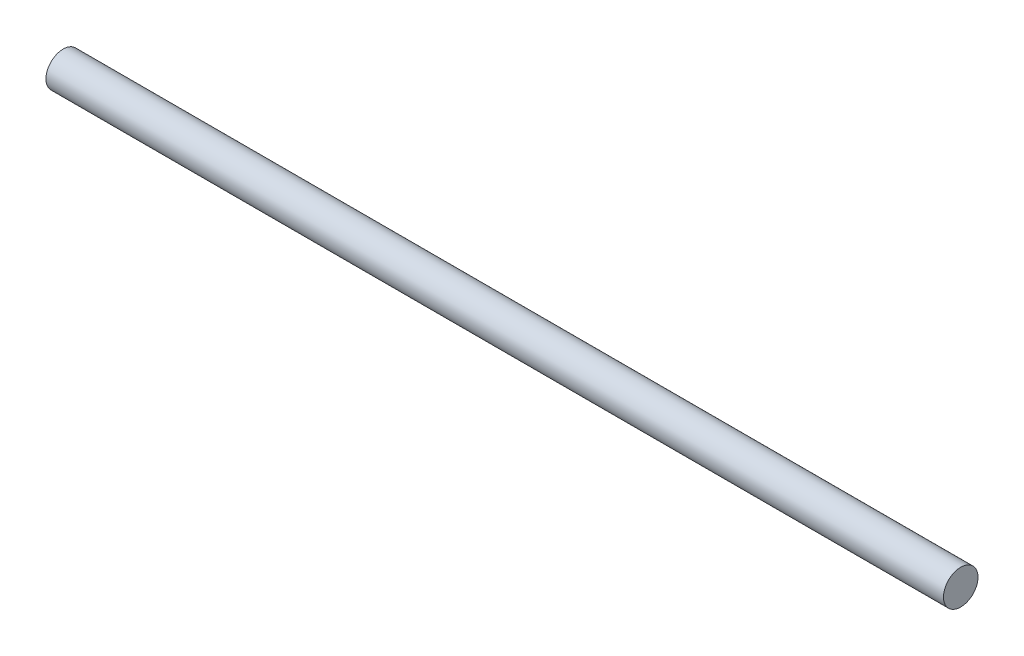
SolidWorks part; units mm, degrees
ref_plane "Płaszczyzna przednia" through (0, 0, 0) normal (0, 0, 1) x (1, 0, 0)
ref_plane "Płaszczyzna górna" through (0, 0, 0) normal (0, 1, 0) x (1, 0, 0)
ref_plane "Płaszczyzna prawa" through (0, 0, 0) normal (1, 0, 0) x (0, 0, -1)
sketch "Sketch1" plane through (0, 0, 0) normal (1, 0, 0) x (0, 0, -1)
  circle A0 centre (0, 0) radius 10
  dimension "D1" = 20
extrude "Boss-Extrude1" add sketch "Sketch1" along normal blind 520
